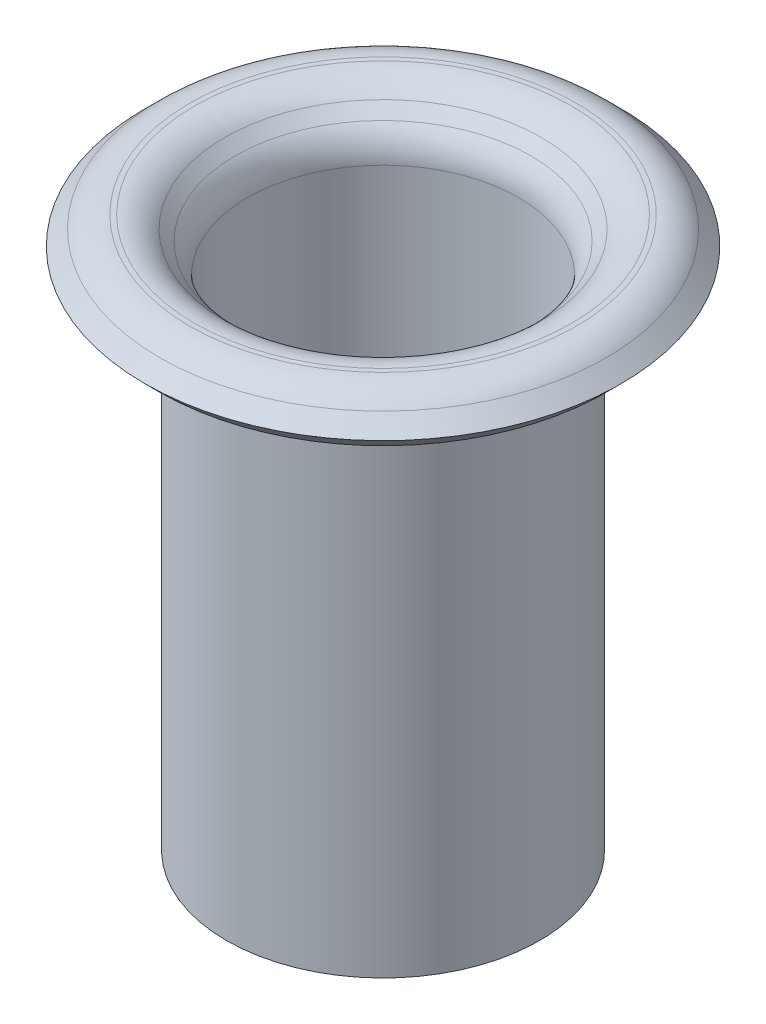
SolidWorks part; units mm, degrees
material "Laiton"
ref_plane "Plan de face" through (0, 0, 0) normal (0, 0, 1) x (1, 0, 0)
ref_plane "Plan de dessus" through (0, 0, 0) normal (0, 1, 0) x (1, 0, 0)
ref_plane "Plan de droite" through (0, 0, 0) normal (1, 0, 0) x (0, 0, -1)
sketch "Esquisse1" plane through (0, 0, 0) normal (0, 0, 1) x (1, 0, 0)
  line L0 (0, 0) -> (0, -2.6969) construction
  line L1 (-1.4972, -0.1172) -> (-1.3972, -0.2172)
  line L2 (-1.48, -0.5) -> (-1.48, -5.2)
  line L3 (-1.8257, 0) -> (-1.78, 0)
  line L4 (-1.28, -0.5) -> (-1.28, -5.2)
  line L5 (-2.25, -0.2586) -> (-2.1086, -0.4)
  line L6 (-1.28, -5.2) -> (-1.48, -5.2)
  line L7 (-2.2556, -0.2) -> (-1.6782, -0.2) construction
  line L8 (-2.1086, -0.1172) -> (-2.25, -0.2586)
  line L9 (-2.1086, -0.4) -> (-1.9672, -0.2586)
  line L10 (-2.2556, 0) -> (-1.6695, 0) construction
  line L11 (-1.8257, -0.2) -> (-1.78, -0.2)
  line L12 (-1.6386, -0.2586) -> (-1.5386, -0.3586)
  line L13 (-1.28, -0.5847) -> (-1.28, -5.2) construction
  line L14 (-1.48, -0.5474) -> (-1.48, -5.2) construction
  arc A0 (-1.9672, -0.2586) -> (-1.8257, -0.2) centre (-1.8257, -0.4) cw
  arc A1 (-1.78, -0.2) -> (-1.6386, -0.2586) centre (-1.78, -0.4) cw
  arc A2 (-1.6695, 0) -> (-1.28, -0.5847) centre (-1.7029, -0.4443) cw construction
  arc A3 (-1.6782, -0.2) -> (-1.48, -0.5474) centre (-1.7029, -0.4443) cw construction
  arc A4 (-1.5386, -0.3586) -> (-1.48, -0.5) centre (-1.68, -0.5) cw
  arc A5 (-2.1086, -0.1172) -> (-1.8257, 0) centre (-1.8257, -0.4) cw
  arc A6 (-1.78, 0) -> (-1.4972, -0.1172) centre (-1.78, -0.4) cw
  arc A7 (-1.3972, -0.2172) -> (-1.28, -0.5) centre (-1.68, -0.5) cw
  dimension "D3" = 0.2
  dimension "D7" = 45
  dimension "D1" = 4.5
  dimension "D2" = 2.96
  dimension "D5" = 5.2
  dimension "D6" = 2.56
  dimension "D8" = 45
  dimension "D9" = 0.4
  dimension "D10" = 0.5
  dimension "D11" = 4.8
  dimension "D4" = 0.2
revolve "Révolution1" add sketch "Esquisse1" angle 360 about L0
